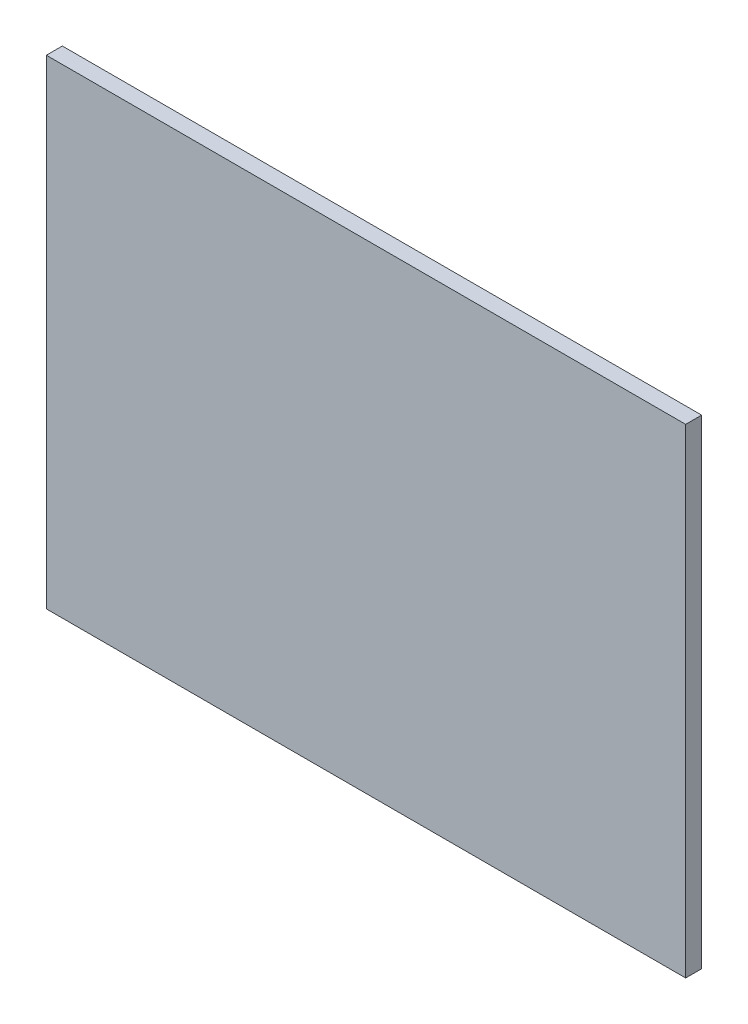
SolidWorks part; units mm, degrees
ref_plane "Front Plane" through (0, 0, 0) normal (0, 0, 1) x (1, 0, 0)
ref_plane "Top Plane" through (0, 0, 0) normal (0, 1, 0) x (1, 0, 0)
ref_plane "Right Plane" through (0, 0, 0) normal (1, 0, 0) x (0, 0, -1)
sketch "Sketch1" plane through (0, 0, 0) normal (0, 0, 1) x (1, 0, 0)
  line L1 (30, -22.5) -> (-30, -22.5)
  line L2 (30, -22.5) -> (30, 22.5)
  line L3 (30, 22.5) -> (-30, 22.5)
  line L4 (-30, -22.5) -> (-30, 22.5)
  line L5 (30, -22.5) -> (-30, 22.5) construction
  line L6 (30, 22.5) -> (-30, -22.5) construction
  point P0 (0, 0)
extrude "Boss-Extrude1" add sketch "Sketch1" along normal blind 1.5
